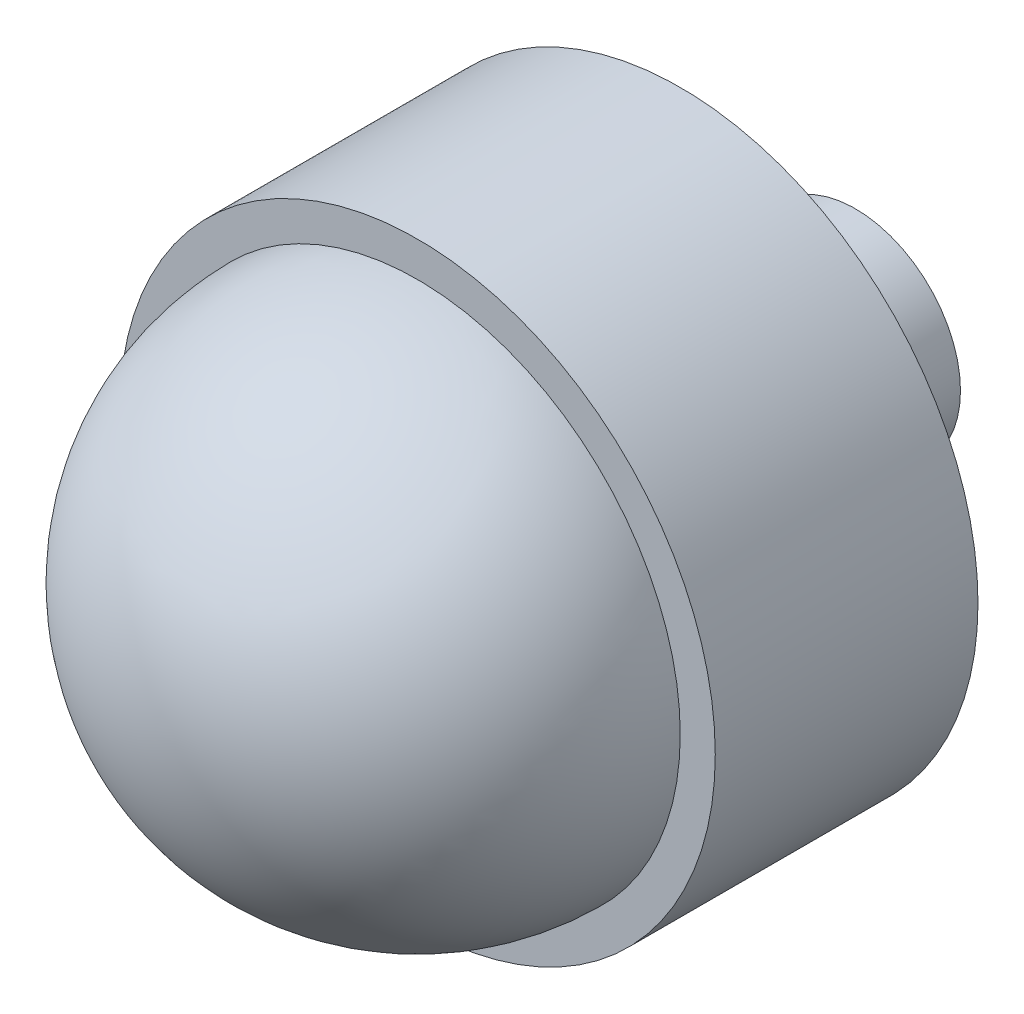
SolidWorks part; units mm, degrees
ref_plane "Front Plane" through (0, 0, 0) normal (0, 0, 1) x (1, 0, 0)
ref_plane "Top Plane" through (0, 0, 0) normal (0, 1, 0) x (1, 0, 0)
ref_plane "Right Plane" through (0, 0, 0) normal (1, 0, 0) x (0, 0, -1)
sketch "Sketch1" plane through (0, 0, 0) normal (0, 1, 0) x (1, 0, 0)
  line L0 (0, 0) -> (0, 77.5482) construction
  line L1 (0, 73.6993) -> (6, 73.6993)
  line L2 (6, 73.6993) -> (6, 63.6993)
  line L3 (17, 48.6993) -> (17, 63.6993)
  line L4 (6, 63.6993) -> (17, 63.6993)
  line L5 (0, 73.6993) -> (0, 33.6993)
  line L6 (17, 48.6993) -> (15, 48.6993)
  arc A0 (0, 33.6993) -> (15, 48.6993) centre (0, 48.6993) ccw
  dimension "D5" = 25
  dimension "D4" = 15
  dimension "D1" = 12
  dimension "D2" = 34
  dimension "D3" = 10
revolve "Revolve6" add sketch "Sketch1" angle 360 about L0
